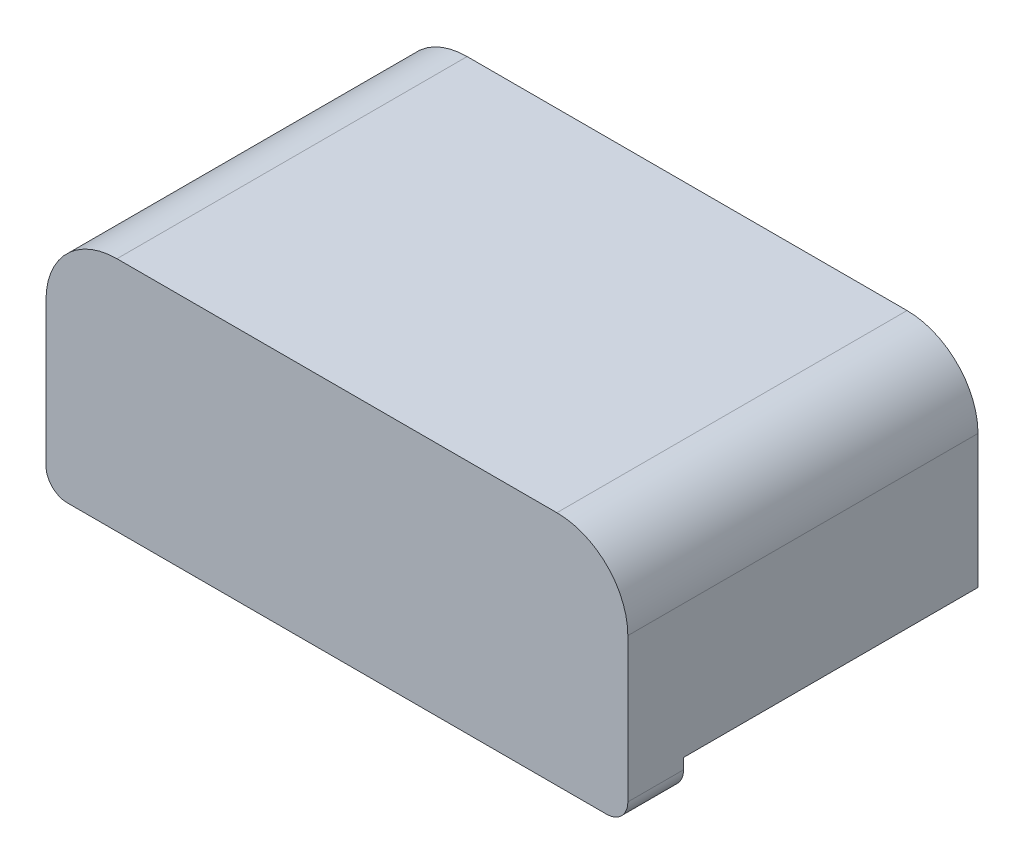
SolidWorks part; units mm, degrees
ref_plane "Front Plane" through (0, 0, 0) normal (0, 0, 1) x (1, 0, 0)
ref_plane "Top Plane" through (0, 0, 0) normal (0, 1, 0) x (1, 0, 0)
ref_plane "Right Plane" through (0, 0, 0) normal (1, 0, 0) x (0, 0, -1)
sketch "Sketch1" plane through (0, 0, 0) normal (0, 0, 1) x (1, 0, 0)
  line L0 (0, -0.45) -> (0, 0) construction
  line L1 (-4.1, -0.45) -> (4.1, -0.45)
  line L2 (-4.1, -0.45) -> (-4.1, 2.88)
  line L3 (-4.1, 2.88) -> (4.1, 2.88)
  line L4 (4.1, -0.45) -> (4.1, 2.88)
  dimension "D1" = 0.45
  dimension "D2" = 8.2
  dimension "D3" = 2.88
extrude "Boss-Extrude1" add sketch "Sketch1" along normal blind 0.785
sketch "Sketch2" plane through (0, 0, 0) normal (0, 0, -1) x (-1, 0, 0)
  line L0 (4.1, 2.88) -> (4.1, -0.45) construction
  line L1 (-4.1, 2.88) -> (4.1, 2.88)
  line L2 (-4.1, 2.88) -> (-4.1, 0)
  line L3 (-4.1, 0) -> (4.1, 0)
  line L4 (4.1, 2.88) -> (4.1, 0)
extrude "Boss-Extrude2" add sketch "Sketch2" along normal offset from surface (4.15 mm away) 4.935 up to face at (0, 1.215, 0.785)
fillet "Fillet1" radius 1 2 edges at (4.1, 2.88, -1.6825) (-4.1, 2.88, -1.6825)
fillet "Fillet2" radius 0.3 2 edges at (4.1, -0.45, 0.3925) (-4.1, -0.45, 0.3925)
